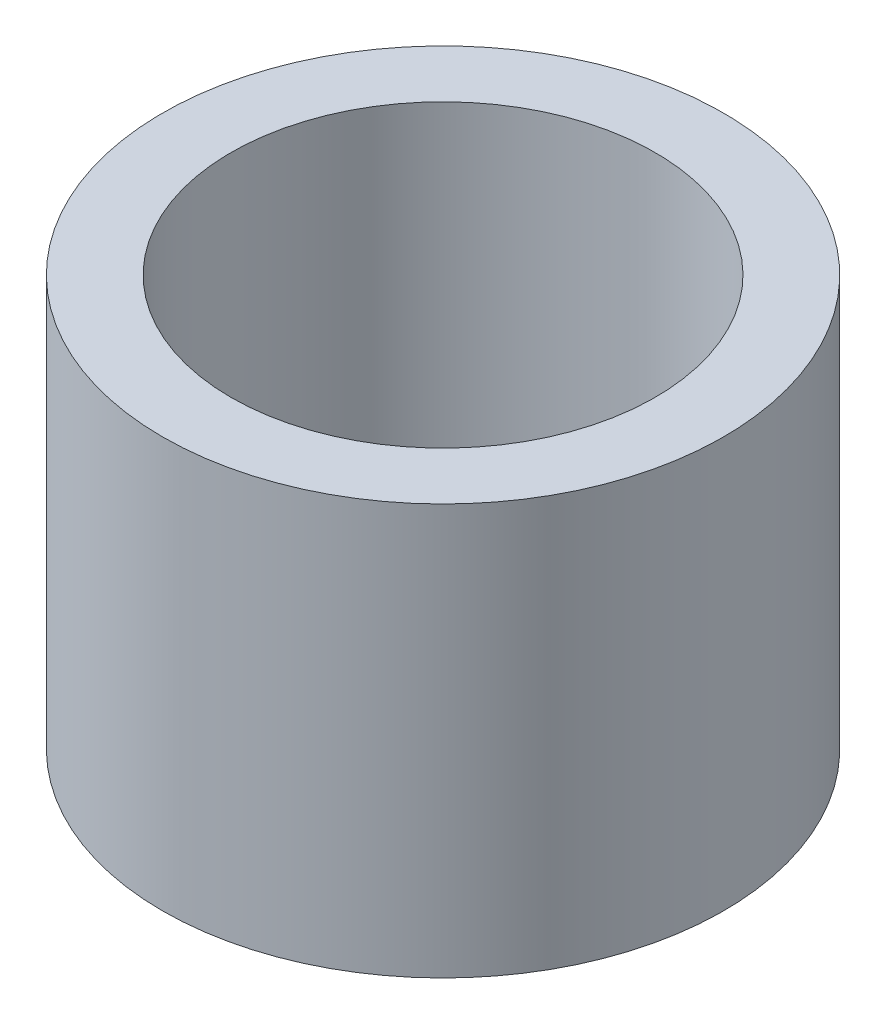
SolidWorks part; units mm, degrees
material "ABS"
ref_plane "Front Plane" through (0, 0, 0) normal (0, 0, 1) x (1, 0, 0)
ref_plane "Top Plane" through (0, 0, 0) normal (0, 1, 0) x (1, 0, 0)
ref_plane "Right Plane" through (0, 0, 0) normal (1, 0, 0) x (0, 0, -1)
sketch "Sketch1" plane through (0, 0, 0) normal (0, 1, 0) x (1, 0, 0)
  circle A0 centre (0, 0) radius 3.1
  circle A1 centre (0, 0) radius 4.1
  dimension "D1" = 1
  dimension "D2" = 6.2
extrude "Boss-Extrude1" add sketch "Sketch1" along normal blind 6
